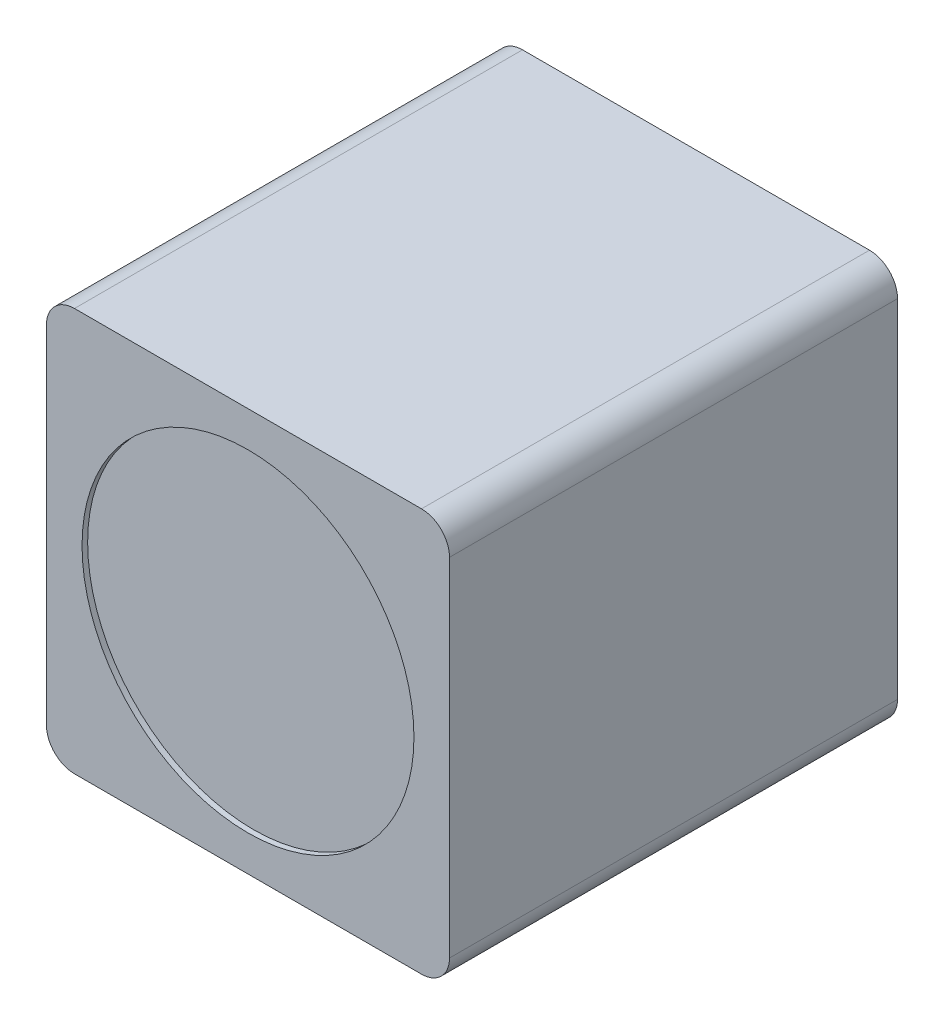
SolidWorks part; units mm, degrees
ref_plane "Front Plane" through (0, 0, 0) normal (0, 0, 1) x (1, 0, 0)
ref_plane "Top Plane" through (0, 0, 0) normal (0, 1, 0) x (1, 0, 0)
ref_plane "Right Plane" through (0, 0, 0) normal (1, 0, 0) x (0, 0, -1)
sketch "Sketch1" plane through (0, 0, 0) normal (0, 0, 1) x (1, 0, 0)
  line L1 (-173.5585, 37.7057) -> (-159.1652, 37.7057)
  line L2 (-173.5585, 37.7057) -> (-173.5585, 52.099)
  line L3 (-173.5585, 52.099) -> (-159.1652, 52.099)
  line L4 (-159.1652, 37.7057) -> (-159.1652, 52.099)
  line L5 (-173.5585, 37.7057) -> (-159.1652, 52.099) construction
  line L6 (-173.5585, 52.099) -> (-159.1652, 37.7057) construction
  point P0 (-166.3618, 44.9023)
  dimension "D1" = 14.3933
extrude "Boss-Extrude1" add sketch "Sketch1" along normal blind 16
fillet "Fillet1" radius 1 4 edges at (-173.5585, 52.099, 8) (-159.1652, 52.099, 8) (-159.1652, 37.7057, 8) (-173.5585, 37.7057, 8)
sketch "Sketch2" plane through (0, 0, 16) normal (0, 0, 1) x (1, 0, 0)
  circle A0 centre (-166.3618, 44.9023) radius 5.9267
  dimension "D1" = 11.8533
extrude "Cut-Extrude1" cut sketch "Sketch2" against normal blind 0.2
